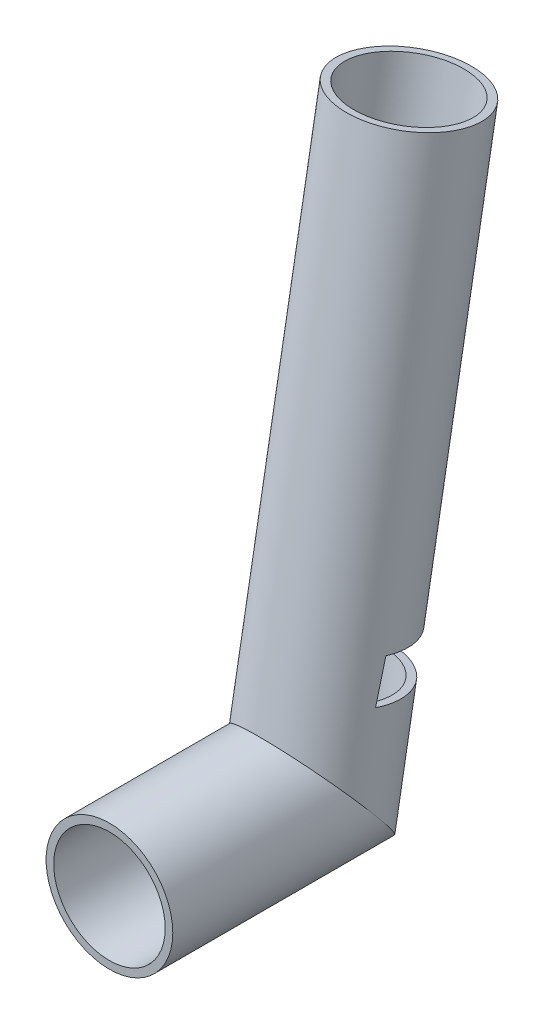
SolidWorks part; units mm, degrees
ref_plane "Front Plane" through (0, 0, 0) normal (0, 0, 1) x (1, 0, 0)
ref_plane "Top Plane" through (0, 0, 0) normal (0, 1, 0) x (1, 0, 0)
ref_plane "Right Plane" through (0, 0, 0) normal (1, 0, 0) x (0, 0, -1)
sketch "Sketch1" plane through (0, 0, 0) normal (1, 0, 0) x (0, 0, -1)
  line L0 (0, 0) -> (80, 0)
  line L1 (80, 0) -> (118.2026, 216.6577)
  line L2 (80, 0) -> (47.2364, 0) construction
  dimension "D1" = 80
sketch "Sketch3" plane through (0, 0, 0) normal (0, 0, 1) x (1, 0, 0)
  circle A0 centre (0, 0) radius 22
  circle A1 centre (0, 0) radius 25
sweep "Sweep1" add profiles "Sketch3" path "Sketch1"
sketch "Sketch4" plane through (0, 0, 0) normal (1, 0, 0) x (0, 0, -1)
  line L0 (80.6522, 36.2695) -> (49.8323, 10.4085)
  line L1 (100.9775, -25) -> (59.0225, 25) construction
  line L3 (100.9775, -25) -> (142.8228, 212.3165) construction
  line L4 (106.3755, 5.6137) -> (109.6107, 23.9612)
  line L7 (62.4102, 20.9627) -> (100.9775, -25)
  line L11 (113.6872, 47.0803) -> (109.6107, 23.9612)
  line L12 (80.6522, 36.2695) -> (110.8423, 30.9462)
  line L13 (80.6522, 36.2695) -> (84.5249, 52.2224)
  line L14 (113.6872, 47.0803) -> (94.7943, 50.4116)
  line L15 (94.7943, 50.4116) -> (84.5249, 52.2224)
extrude "Cut-Extrude2" cut sketch "Sketch4" against normal through all both and the other way through all
